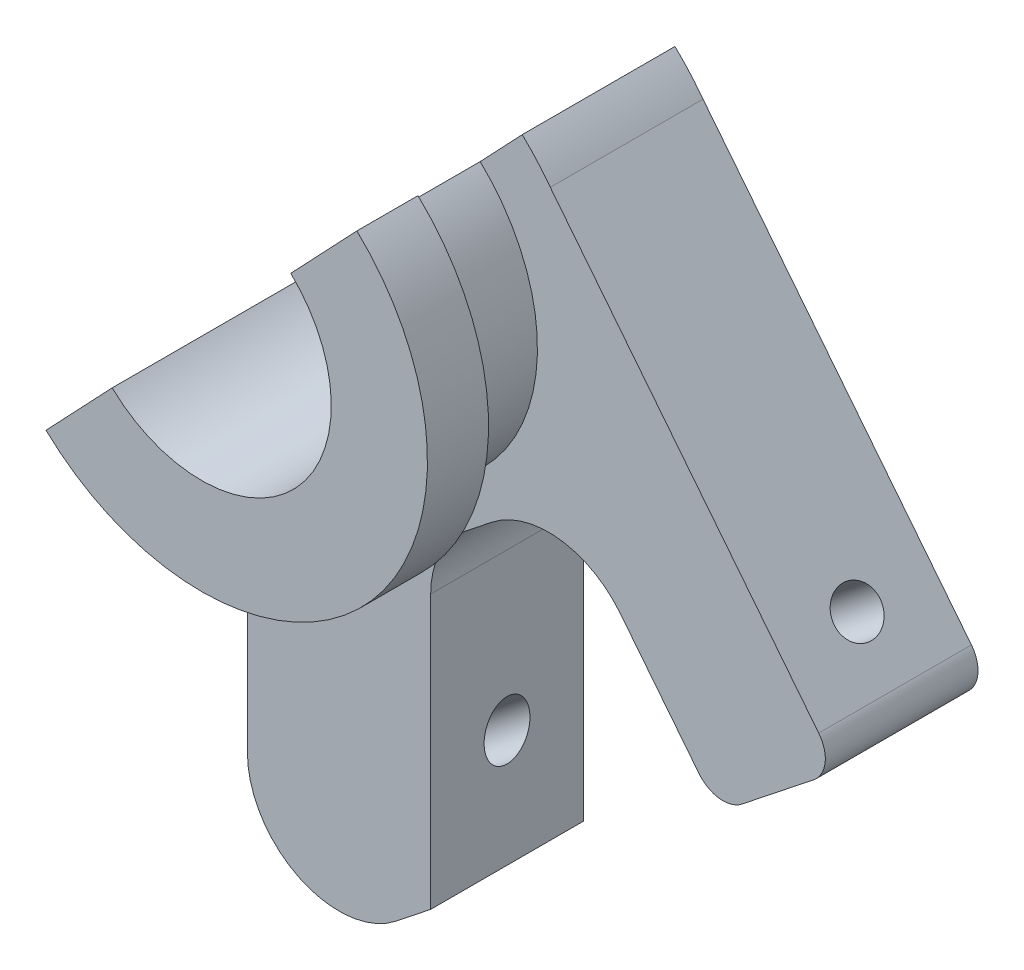
SolidWorks part; units mm, degrees
ref_plane "Front Plane" through (0, 0, 0) normal (0, 0, 1) x (1, 0, 0)
ref_plane "Top Plane" through (0, 0, 0) normal (0, 1, 0) x (1, 0, 0)
ref_plane "Right Plane" through (0, 0, 0) normal (1, 0, 0) x (0, 0, -1)
sketch "Skica1" plane through (0, 0, 0) normal (0, 0, 1) x (1, 0, 0)
  line L0 (-3.4956, -2.4173) -> (-3.4956, -22.4173)
  line L1 (-3.4956, -22.4173) -> (2.5044, -22.4173)
  line L2 (2.5044, -22.4173) -> (2.5044, -7.267)
  line L3 (-3.4956, -22.4173) -> (38.4945, 10.8828) construction
  line L4 (2.5044, -7.267) -> (6.8524, -3.8189)
  line L5 (6.8524, -3.8189) -> (14.3973, -13.3326)
  line L6 (1.6604, 3.9123) -> (4.9746, 6.2653)
  line L7 (14.3973, -13.3326) -> (18.3149, -10.2258)
  line L8 (18.3149, -10.2258) -> (6.4212, 4.7717)
  circle A0 centre (0, 0) radius 4.25
  arc A1 (6.4212, 4.7717) -> (4.9746, 6.2653) centre (0, 0) ccw
  point P4 (49.0781, 11.3567)
  point P11 (27.1263, 8.2516)
  point P16 (0, 0)
  point P17 (29.7207, 8.9867)
  point P18 (0, 0)
  point P19 (-2.0879, -15.7018)
  point P20 (39.6634, 17.4089)
  point P21 (0, 0)
  point P22 (0, 0)
  dimension "D1" = 8.5
  dimension "D2" = 8
  dimension "D3" = 6
  dimension "D4" = 5
  dimension "D5" = 3
  dimension "D6" = 20
  dimension "D7" = 4
extrude "Přidat vysunutím1" add sketch "Skica1" along normal blind 5
sketch "Skica2" plane through (0, 0, 5) normal (0, 0, 1) x (1, 0, 0)
  circle A0 centre (0, 0) radius 4.25
  circle A1 centre (0, 0) radius 6
  dimension "D1" = 12
extrude "Přidat vysunutím2" add sketch "Skica2" along normal blind 3
sketch "Skica3" plane through (0, 0, 8) normal (0, 0, 1) x (1, 0, 0)
  circle A0 centre (0, 0) radius 4.25
  circle A1 centre (0, 0) radius 7.3991
extrude "Přidat vysunutím3" add sketch "Skica3" along normal blind 2
sketch "Skica4" plane through (0, 0, 10) normal (0, 0, 1) x (1, 0, 0)
  line L0 (7.9227, 8.3612) -> (-6.9238, -7.3071)
  line L1 (-6.9238, -7.3071) -> (-16.6477, 7.7172)
  line L2 (-16.6477, 7.7172) -> (7.9227, 8.3612)
extrude "Odebrat vysunutím1" cut sketch "Skica4" against normal blind 12
sketch "Skica5" plane through (6.2651, 4.9685, 0) normal (0.7835, 0.6214, 0) x (0, 0, -1)
  line L0 (-2.5, -15.3924) -> (-2.5, -12.3924) construction
  line L1 (-5, -15.3924) -> (0, -15.3924) construction
  circle A0 centre (-2.5, -12.3924) radius 0.75
  dimension "D1" = 1.5
  dimension "D2" = 3
extrude "Odebrat vysunutím2" cut sketch "Skica5" against normal blind 22
sketch "Skica7" plane through (0, 0, 5) normal (0, 0, 1) x (1, 0, 0)
  line L0 (1.3685, -18.5599) -> (2.5044, -26.1245)
  line L1 (2.5044, -26.1245) -> (-8.0026, -24.0195)
  line L2 (-8.0026, -24.0195) -> (-5.3964, -16.2093)
  line L3 (-5.3964, -16.2093) -> (-3.4956, -16.2093)
  line L8 (5.5025, 5.8071) -> (4.1269, 4.3553)
  line L9 (-3.4956, -4.8766) -> (-3.4956, -22.4173)
  line L10 (-3.4956, -22.4173) -> (2.5044, -17.659)
  line L11 (2.5044, -17.659) -> (2.5044, -7.267)
  line L12 (2.5044, -7.267) -> (6.8524, -3.8189)
  line L13 (6.8524, -3.8189) -> (11.9118, -10.1986)
  line L14 (11.9118, -10.1986) -> (15.8294, -7.0917)
  line L15 (15.8294, -7.0917) -> (6.4212, 4.7717)
  line L16 (5.5025, 5.8071) -> (4.1269, 4.3553)
  line L17 (-3.4956, -4.8766) -> (-3.4956, -16.2093)
  line L18 (1.3685, -18.5599) -> (2.5044, -17.659)
  line L19 (2.5044, -17.659) -> (2.5044, -7.267)
  line L20 (2.5044, -7.267) -> (6.8524, -3.8189)
  line L21 (6.8524, -3.8189) -> (11.9118, -10.1986)
  line L22 (11.9118, -10.1986) -> (15.8294, -7.0917)
  line L23 (15.8294, -7.0917) -> (6.4212, 4.7717)
  arc A0 (-3.4956, -16.2093) -> (1.3685, -18.5599) centre (-0.4956, -16.2093) ccw
  arc A2 (-3.4956, -4.8766) -> (4.1269, 4.3553) centre (0, 0) ccw
  arc A3 (6.4212, 4.7717) -> (5.5025, 5.8071) centre (0, 0) ccw
  arc A4 (-3.4956, -4.8766) -> (4.1269, 4.3553) centre (0, 0) ccw
  arc A5 (6.4212, 4.7717) -> (5.5025, 5.8071) centre (0, 0) ccw
  line M13 (-3.4956, -4.8766) -> (-3.4956, -22.4173)
  line M14 (-3.4956, -22.4173) -> (2.5044, -17.659)
  dimension "D2" = 3
  dimension "D1" = 0
extrude "Odebrat vysunutím3" cut sketch "Skica7" against normal blind 22 contours A0 M13 M14
fillet "Zaoblit1" radius 3 2 edges at (2.5044, -7.267, 2.5) (6.8524, -3.8189, 2.5)
fillet "Zaoblit2" radius 1 2 edges at (15.8294, -7.0917, 2.5) (11.9118, -10.1986, 2.5)
